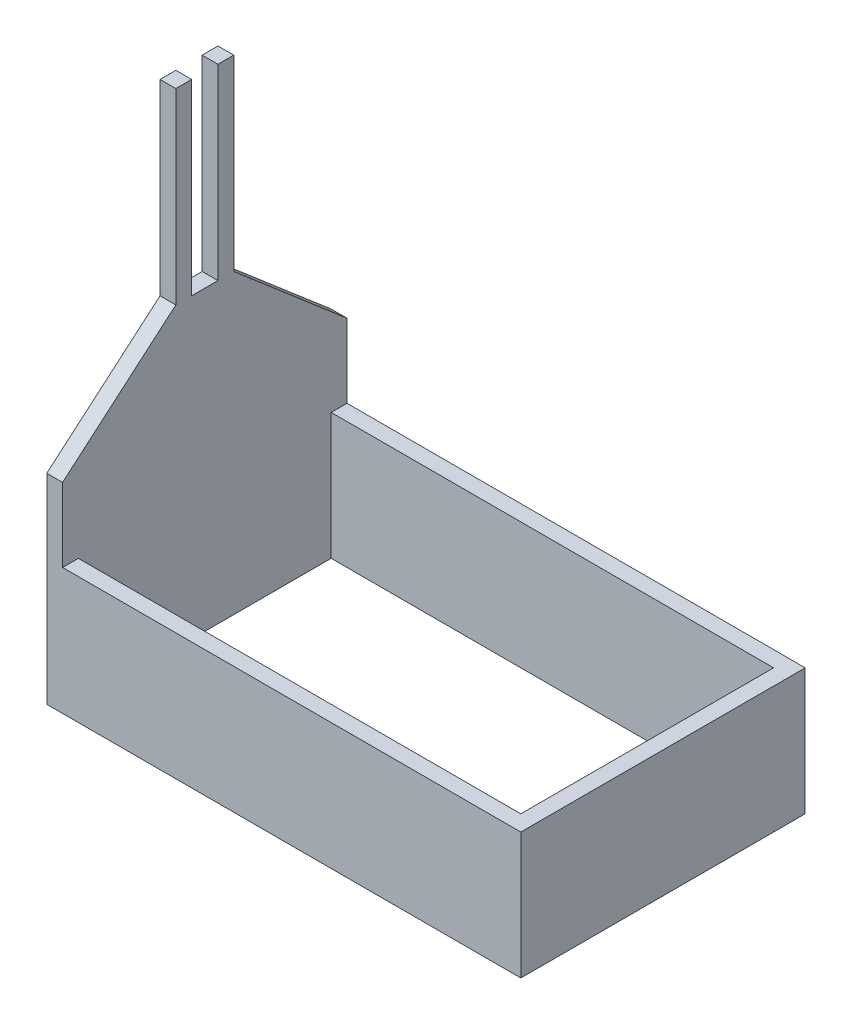
SolidWorks part; units mm, degrees
ref_plane "Front Plane" through (0, 0, 0) normal (0, 0, 1) x (1, 0, 0)
ref_plane "Top Plane" through (0, 0, 0) normal (0, 1, 0) x (1, 0, 0)
ref_plane "Right Plane" through (0, 0, 0) normal (1, 0, 0) x (0, 0, -1)
sketch "Sketch1" plane through (0, 0, 0) normal (0, 1, 0) x (1, 0, 0)
  line L1 (0, 0) -> (2286, 0)
  line L2 (0, 0) -> (0, 1371.6)
  line L3 (0, 1371.6) -> (2286, 1371.6)
  line L4 (2286, 0) -> (2286, 1371.6)
  dimension "D1" = 2286
  dimension "D2" = 1371.6
extrude "Boss-Extrude1" add sketch "Sketch1" along normal blind 609.6
sketch "Sketch2" plane through (0, 609.6, 0) normal (0, 1, 0) x (1, 0, 0)
  line L0 (2286, 1371.6) -> (0, 1371.6) construction
  line L1 (76.2, 1295.4) -> (2209.8, 1295.4)
  line L2 (76.2, 1295.4) -> (76.2, 76.2)
  line L3 (76.2, 76.2) -> (2209.8, 76.2)
  line L4 (2209.8, 1295.4) -> (2209.8, 76.2)
  line L5 (0, 1371.6) -> (0, 0) construction
  dimension "D1" = 2133.6
  dimension "D2" = 1219.2
  dimension "D3" = 76.2
  dimension "D4" = 76.2
extrude "Cut-Extrude1" cut sketch "Sketch2" against normal blind 609.6
sketch "Sketch3" plane through (0, 609.6, 0) normal (0, 1, 0) x (1, 0, 0)
  line L0 (0, 0) -> (2286, 0) construction
  line L1 (0, 1371.6) -> (76.2, 1371.6)
  line L2 (0, 1371.6) -> (0, 0)
  line L3 (0, 0) -> (76.2, 0)
  line L4 (76.2, 1371.6) -> (76.2, 0)
  dimension "D1" = 76.2
extrude "Boss-Extrude3" add sketch "Sketch3" along normal blind 1727.2
sketch "Sketch4" plane through (0, 0, 0) normal (-1, 0, 0) x (0, 0, 1)
  line L0 (-1371.6, 609.5146) -> (0, 609.5146) construction
  line L1 (-1371.6, 2336.8) -> (-1371.6, 0) construction
  line L2 (0, 2336.8) -> (0, 0) construction
  line L3 (-1371.6, 965.1146) -> (0, 965.1146) construction
  line L4 (-1371.6, 965.1146) -> (-825.5, 1433.157) construction
  line L5 (0, 965.1146) -> (-546.1, 1433.157) construction
  line L6 (-1371.6, 965.1146) -> (-825.5, 1433.157)
  line L7 (-825.5, 1433.157) -> (-825.5, 2336.8)
  line L8 (-1371.6, 2336.8) -> (0, 2336.8) construction
  dimension "D1" = 355.6
  dimension "D2" = 546.1
  dimension "D3" = 546.1
extrude "Cut-Extrude2" cut sketch "Sketch4" against normal blind 1727.2 and the other way through all
sketch "Sketch5" plane through (0, 0, 0) normal (-1, 0, 0) x (0, 0, 1)
  line L0 (-1371.6, 965.1146) -> (0, 965.1146) construction
  line L1 (0, 2336.8) -> (0, 0) construction
  line L2 (0, 965.1146) -> (-546.1, 1433.157) construction
  line L3 (-825.5, 2336.8) -> (-749.3, 2336.8)
  line L4 (-825.5, 2336.8) -> (0, 2336.8) construction
  line L5 (-749.3, 2336.8) -> (-749.3, 1433.157)
  line L6 (-749.3, 1433.157) -> (-622.3, 1433.157)
  line L7 (-622.3, 1433.157) -> (-622.3, 2336.8)
  line L8 (-622.3, 2336.8) -> (-546.1, 2336.8)
  line L9 (-546.1, 2336.8) -> (-546.1, 1433.157)
  line L10 (-546.1, 1433.157) -> (0, 965.1146)
  dimension "D1" = 546.1
  dimension "D2" = 76.2
  dimension "D3" = 127
  dimension "D4" = 76.2
extrude "Cut-Extrude3" cut sketch "Sketch5" against normal blind 1727.2 and the other way through all
